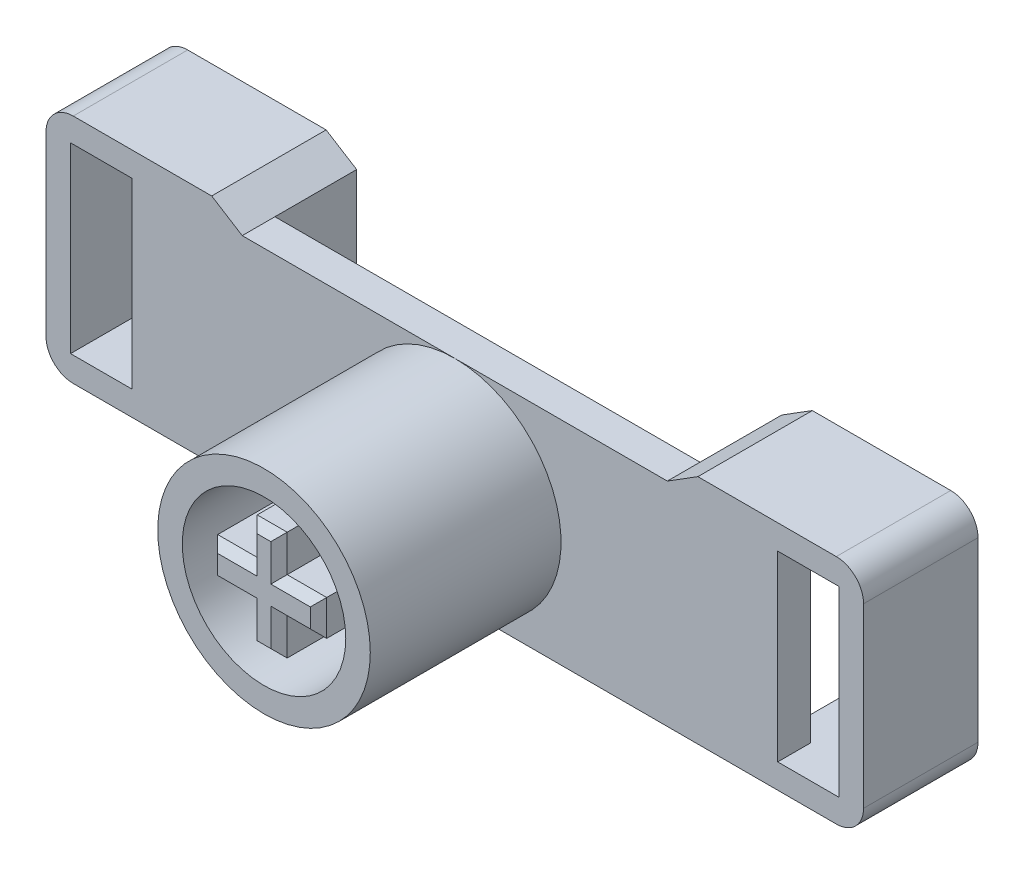
SolidWorks part; units mm, degrees
ref_plane "Front Plane" through (0, 0, 0) normal (0, 0, 1) x (1, 0, 0)
ref_plane "Top Plane" through (0, 0, 0) normal (0, 1, 0) x (1, 0, 0)
ref_plane "Right Plane" through (0, 0, 0) normal (1, 0, 0) x (0, 0, -1)
sketch "Sketch1" plane through (0, 0, 0) normal (0, 0, 1) x (1, 0, 0)
  line L0 (0, -1000) -> (0, 49000) construction
  line L1 (-1000, 0) -> (49000, 0) construction
  line L4 (-2, -0.65) -> (2, -0.65)
  line L5 (-2, -0.65) -> (-2, 0.65)
  line L6 (-2, 0.65) -> (2, 0.65)
  line L7 (2, -0.65) -> (2, 0.65)
  line L8 (-2, -0.65) -> (2, 0.65) construction
  line L9 (-2, 0.65) -> (2, -0.65) construction
  line L10 (-0.55, -2) -> (0.55, -2)
  line L11 (-0.55, -2) -> (-0.55, 2)
  line L12 (-0.55, 2) -> (0.55, 2)
  line L13 (0.55, -2) -> (0.55, 2)
  line L14 (-0.55, -2) -> (0.55, 2) construction
  line L15 (-0.55, 2) -> (0.55, -2) construction
  circle A0 centre (0, 0) radius 3.9
  circle A1 centre (0, 0) radius 3
  dimension "D1" = 7.8
  dimension "D2" = 6
  dimension "D3" = 4
  dimension "D4" = 1.3
  dimension "D5" = 1.1
  dimension "D6" = 4
extrude "Boss-Extrude1" add sketch "Sketch1" along normal blind 7 contours L6 L13 L12 L11 | L13 L4 L7 L6 | L4 L13 L6 L11 | L10 L13 L4 L11 | L4 L11 L6 L5 | A0 A1
sketch "Sketch2" plane through (0, 0, 0) normal (0, 0, 1) x (1, 0, 0)
  circle A0 centre (0, 0) radius 3
  dimension "D1" = 6
extrude "Boss-Extrude2" add sketch "Sketch2" along normal blind 3
sketch "Sketch3" plane through (0, 0, 0) normal (0, 0, 1) x (1, 0, 0)
  line L0 (0, -1000) -> (0, 49000) construction
  line L1 (-1000, 0) -> (49000, 0) construction
  line L2 (-2, 2) -> (-0.55, 2)
  line L3 (-2, 2) -> (-2, 0.65)
  line L4 (-2, 0.65) -> (-0.55, 0.65)
  line L5 (-0.55, 2) -> (-0.55, 0.65)
  line L7 (0.55, 0.65) -> (2, 0.65) construction
  line L8 (0.55, 0.65) -> (0.55, 2) construction
  line L9 (0.55, 2) -> (2, 2) construction
  line L10 (2, 0.65) -> (2, 2) construction
  line L11 (-2, -2) -> (-0.55, -2) construction
  line L12 (-2, -2) -> (-2, -0.65) construction
  line L13 (-2, -0.65) -> (-0.55, -0.65) construction
  line L14 (-0.55, -2) -> (-0.55, -0.65) construction
  line L15 (0.55, -0.65) -> (2, -0.65)
  line L16 (0.55, -0.65) -> (0.55, -2)
  line L17 (0.55, -2) -> (2, -2)
  line L18 (2, -0.65) -> (2, -2)
  dimension "D5" = 1.1
  dimension "D1" = 2
  dimension "D2" = 2
  dimension "D3" = 0.55
  dimension "D4" = 0.65
  dimension "D6" = 1.3
  dimension "D7" = 1.3
sketch "Sketch4" plane through (0, 0, 0) normal (0, 0, 1) x (1, 0, 0)
  line L0 (-1000, 0) -> (49000, 0) construction
  line L1 (0, -1000) -> (0, 49000) construction
  line L2 (-15, 3.9) -> (-15, 4.6)
  line L3 (-15, -3.9) -> (15, -3.9)
  line L4 (-15, -3.9) -> (-15, 3.9)
  line L5 (-15, 3.9) -> (15, 3.9)
  line L6 (15, -3.9) -> (15, 3.9)
  line L7 (-15, -3.9) -> (15, 3.9) construction
  line L8 (-15, 3.9) -> (15, -3.9) construction
  line L9 (15, 3.9) -> (15, 4.6)
  line L10 (-8.9202, 4.6) -> (-7.8, 3.9)
  line L11 (8.9202, 4.6) -> (7.8, 3.9)
  line L12 (-15, 4.6) -> (-8.9202, 4.6)
  line L13 (15, 4.6) -> (8.9202, 4.6)
  point P4 (0, 0)
  dimension "D1" = 7.8
  dimension "D2" = 30
  dimension "D3" = 8.5
  dimension "D4" = 7.2
  dimension "D5" = 32
extrude "Boss-Extrude3" add sketch "Sketch4" against normal blind 4.2 contours L12 L2 L5 L10 | L3 L6 L5 L4 | L9 L13 L11 L5
extrude "Cut-Extrude3" cut sketch "Sketch3" against normal through all both and the other way through all
sketch "Sketch5" plane through (0, 0, -4.2) normal (0, 0, -1) x (-1, 0, 0)
  line L1 (7.8, 3.9) -> (-7.8, 3.9)
  line L2 (7.8, 3.9) -> (7.8, -3.9)
  line L3 (7.8, -3.9) -> (-7.8, -3.9)
  line L4 (-7.8, 3.9) -> (-7.8, -3.9)
  line L5 (7.8, 3.9) -> (-7.8, -3.9) construction
  line L6 (7.8, -3.9) -> (-7.8, 3.9) construction
  point P0 (0, 0)
  dimension "D1" = 7.8
  dimension "D2" = 15.6
extrude "Cut-Extrude4" cut sketch "Sketch5" against normal blind 3
sketch "Sketch6" plane through (0, 0, 0) normal (0, 0, 1) x (1, 0, 0)
  line L0 (0, -1000) -> (0, 49000) construction
  line L1 (-1000, 0) -> (49000, 0) construction
  line L2 (14.1, 3.7) -> (14.1, -3)
  line L3 (-14.1, 3.7) -> (-11.85, 3.7)
  line L4 (-14.1, 3.7) -> (-14.1, -3)
  line L5 (-14.1, -3) -> (-11.85, -3)
  line L6 (-11.85, 3.7) -> (-11.85, -3)
  line L7 (14.1, 3.7) -> (11.85, 3.7)
  line L8 (11.85, 3.7) -> (11.85, -3)
  line L9 (14.1, -3) -> (11.85, -3)
  line L10 (-15, -3.9) -> (-15, 4.6) construction
  line L11 (-15, 4.6) -> (-8.9202, 4.6) construction
  line L12 (-15, -3.9) -> (0, -3.9) construction
  dimension "D2" = 0.9
  dimension "D3" = 0.9
  dimension "D4" = 0.9
  dimension "D1" = 2.25
extrude "Cut-Extrude5" cut sketch "Sketch6" against normal blind 3
sketch "Sketch7" plane through (0, 0, -4.2) normal (0, 0, -1) x (-1, 0, 0)
  line L0 (0, -1000) -> (0, 49000) construction
  line L1 (-1000, 0) -> (49000, 0) construction
  line L2 (12.06, -3) -> (10.95, -3)
  line L3 (-8.7, 3.7) -> (-14.1, 3.7)
  line L4 (-8.7, 3.7) -> (-8.7, -3.9)
  line L5 (-8.7, -3.9) -> (-10.95, -3.9)
  line L6 (-15, -3.9) -> (-15, 4.6) construction
  line L7 (12.06, 1.7) -> (12.06, -3)
  line L8 (-14.1, 3.7) -> (-14.1, 1.7)
  line L9 (14.1, 1.7) -> (12.06, 1.7)
  line L10 (-15, 4.6) -> (-8.9202, 4.6) construction
  line L11 (-7.8, 3.9) -> (-7.8, -3.9) construction
  line L12 (10.95, -3.9) -> (10.95, -3)
  line L13 (-7.8, -3.9) -> (-15, -3.9) construction
  line L14 (-10.95, -3.9) -> (-10.95, -3)
  line L15 (14.1, 3.7) -> (14.1, 1.7)
  line L16 (-14.1, 1.7) -> (-12.06, 1.7)
  line L17 (8.7, -3.9) -> (10.95, -3.9)
  line L18 (8.7, 3.7) -> (8.7, -3.9)
  line L19 (-12.06, 1.7) -> (-12.06, -3)
  line L20 (8.7, 3.7) -> (14.1, 3.7)
  line L21 (-12.06, -3) -> (-10.95, -3)
  dimension "D4" = 0.9
  dimension "D1" = 0.9
  dimension "D2" = 0.9
  dimension "D3" = 2.25
  dimension "D5" = 2
  dimension "D6" = 0.9
  dimension "D7" = 2.04
extrude "Cut-Extrude6" cut sketch "Sketch7" against normal blind 3
sketch "Sketch8" plane through (0, 0, -1.2) normal (0, 0, -1) x (-1, 0, 0)
  line L0 (0, -1000) -> (0, 49000) construction
  line L1 (-1000, 0) -> (49000, 0) construction
  line L2 (-8.7, 3.7) -> (-11.85, 3.7) construction
  line L3 (-8.7, 3.7) -> (-10.95, 3.7)
  line L4 (-8.7, 3.7) -> (-8.7, -3.9)
  line L5 (-8.7, -3.9) -> (-10.95, -3.9)
  line L6 (-10.95, 3.7) -> (-10.95, -3.9)
  line L7 (-8.7, -3.9) -> (-8.7, 3.7) construction
  line L8 (-10.95, -3.9) -> (-8.7, -3.9) construction
  line L9 (10.95, 3.7) -> (10.95, -3.9)
  line L10 (8.7, -3.9) -> (10.95, -3.9)
  line L11 (8.7, 3.7) -> (8.7, -3.9)
  line L12 (8.7, 3.7) -> (10.95, 3.7)
extrude "Cut-Extrude7" cut sketch "Sketch8" against normal blind 0.4
fillet "Fillet1" radius 1 4 edges at (-15, 4.6, -2.1) (-15, -3.9, -2.1) (15, -3.9, -2.1) (15, 4.6, -2.1)
chamfer "Chamfer1" distance 0.3 angle 45 12 edges at (-0.55, 1.325, 7) (0, 2, 7) (0.55, 1.325, 7) (1.275, 0.65, 7) (2, 0, 7) (1.275, -0.65, 7) (0.55, -1.325, 7) (0, -2, 7) (-0.55, -1.325, 7) (-1.275, -0.65, 7) (-2, 0, 7) (-1.275, 0.65, 7)
equation "\"Cherry Outter Diameter\"=7.8"
equation "\"Cherry Inner Diameter\"= 6"
equation "\"Cherry Horizontal Bar Width\"= 1.3"
equation "\"Cherry Horizontal Bar Length\"= 4"
equation "\"Cherry Vertical Bar Width\"=1.1"
equation "\"Cherry Vertical Bar Length\"= 4"
equation "\"Cherry Cylinder Height\"= 7"
equation "\"Cherry Inner Wall Height\"= 3"
equation "\"D1@Sketch1\"=\"Cherry Outter Diameter\""
equation "\"D2@Sketch1\"=\"Cherry Inner Diameter\""
equation "\"D3@Sketch1\"=\"Cherry Horizontal Bar Length\""
equation "\"D4@Sketch1\"=\"Cherry Horizontal Bar Width\""
equation "\"D5@Sketch1\"=\"Cherry Vertical Bar Width\""
equation "\"D1@Boss-Extrude1\"=\"Cherry Cylinder Height\""
equation "\"D1@Sketch2\"=\"Cherry Inner Diameter\""
equation "\"D1@Boss-Extrude2\"=\"Cherry Inner Wall Height\""
equation "\"D1@Sketch3\"=\"Cherry Vertical Bar Length\"/2"
equation "\"D4@Sketch3\"=\"Cherry Horizontal Bar Width\"/2"
equation "\"D3@Sketch3\"=\"Cherry Vertical Bar Width\"/2"
equation "\"D2@Sketch3\"=\"Cherry Horizontal Bar Length\"/2"
equation "\"Base Length\"= 30"
equation "\"Base Width\"= 8.5"
equation "\"Base Side Rect Width\"= 7.2"
equation "\"D1@Sketch4\"=\"Base Inner Width\""
equation "\"D2@Sketch4\"=\"Base Length\""
equation "\"D3@Sketch4\"=\"Base Width\""
equation "\"Base Side Rect Angle\"= 32"
equation "\"D5@Sketch4\"=\"Base Side Rect Angle\""
equation "\"D4@Sketch4\"=\"Base Side Rect Width\""
equation "\"D5@Sketch3\"=\"Cherry Vertical Bar Width\""
equation "\"D6@Sketch3\"=\"Cherry Horizontal Bar Width\""
equation "\"D7@Sketch3\"=\"Cherry Horizontal Bar Width\""
equation "\"Base Height\"= 4.2"
equation "\"D1@Boss-Extrude3\"=\"Base Height\""
equation "\"D1@Sketch5\"=\"Base Inner Width\""
equation "\"D2@Sketch5\"=\"Base Length\"-\"Base Side Rect Width\"*2"
equation "\"Base Inner Width\"= \"Cherry Outter Diameter\""
equation "\"Base Center Cut Out Height\"= 3"
equation "\"D1@Cut-Extrude4\"=\"Base Center Cut Out Height\""
equation "\"Base Basic Thickness\"= 1.2"
equation "\"Base Wall Thickness\"= 0.9"
equation "\"D2@Sketch6\"=\"Base Wall Thickness\""
equation "\"D3@Sketch6\"=\"Base Wall Thickness\""
equation "\"D4@Sketch6\"=\"Base Wall Thickness\""
equation "\"D1@Sketch6\"=(\"Base Side Rect Width\"-3 * \"Base Wall Thickness\")/2"
equation "\"D1@Cut-Extrude5\"=\"Base Center Cut Out Height\""
equation "\"D1@Sketch7\"=\"Base Wall Thickness\""
equation "\"D2@Sketch7\"=\"Base Wall Thickness\""
equation "\"D3@Sketch7\"=(\"Base Side Rect Width\"-3 * \"Base Wall Thickness\")/2"
equation "\"D4@Sketch7\"=\"Base Wall Thickness\""
equation "\"Base String Entry Width\"= 2"
equation "\"D5@Sketch7\"=\"Base String Entry Width\""
equation "\"D6@Sketch7\"=\"Base Wall Thickness\""
equation "\"D7@Sketch7\"=((\"Base Inner Width\" - 3 * \"Base Wall Thickness\")/2)*0.8"
equation "\"Base Inner Further Extrude Thickness\"= 0.4"
equation "\"D1@Cut-Extrude7\"=\"Base Inner Further Extrude Thickness\""
